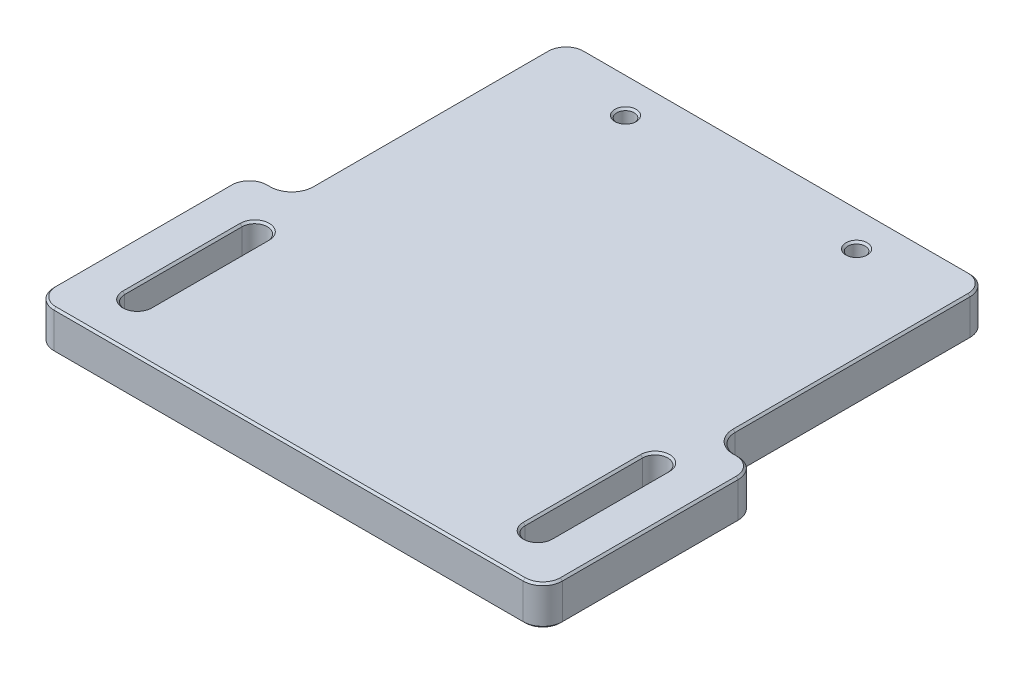
SolidWorks part; units mm, degrees
material "6061-T6 Al"
ref_plane "Front" through (0, 0, 0) normal (0, 0, 1) x (1, 0, 0)
ref_plane "Top" through (0, 0, 0) normal (0, 1, 0) x (1, 0, 0)
ref_plane "Right" through (0, 0, 0) normal (1, 0, 0) x (0, 0, -1)
sketch "Sketch1" plane through (0, 0, 0) normal (0, 1, 0) x (1, 0, 0)
  line L1 (0, 0) -> (-66, 0)
  line L2 (0, 0) -> (0, 63.5)
  line L3 (0, 63.5) -> (-66, 63.5)
  line L4 (-66, 0) -> (-66, 63.5)
  dimension "D1" = 66
  dimension "D2" = 63.5
extrude "Boss-Extrude1" add sketch "Sketch1" along normal blind 5.08
hole_wizard "#4 Clearance Hole1" positions "Sketch4" profile "Sketch3" hole size "#4" standard "Ansi Inch"
sketch "Sketch4" plane through (0, 5.08, 0) normal (0, 1, 0) x (-1, 0, 0)
  line L0 (66, 0) -> (0, 0) construction
  point P0 (59, -6.35)
  point P1 (7, -6.35)
  point P4 (33, 0)
  point P7 (33, 0)
  dimension "D1" = 26
  dimension "D2" = 26
  dimension "D3" = 6.35
sketch "Sketch3" plane through (-59, 5.08, -6.35) normal (1, 0, 0) x (0, 0, 1)
  line L0 (0, 0) -> (0, 26.3806)
  line L1 (0, 26.3806) -> (1.6319, 25.4)
  line L2 (1.6319, 25.4) -> (1.6319, 0)
  line L5 (1.6319, 0) -> (0, 0)
  line L10 (0, 26.3806) -> (-1.632, 25.4) construction
  line L11 (0, -6.35) -> (0, 107.95) construction
  dimension "Hole Dia." = 3.2639
  dimension "Hole Depth" = 25.4
  dimension "Drill Angle" = 118
sketch "Sketch6" plane through (0, 5.08, 0) normal (0, 1, 0) x (1, 0, 0)
  line L1 (-66, 63.5) -> (-60.5, 63.5)
  line L2 (-66, 63.5) -> (-66, 27.9109)
  line L3 (-66, 27.9109) -> (-60.5, 27.9109)
  line L4 (-60.5, 63.5) -> (-60.5, 27.9109)
  line L5 (0, 63.5) -> (-5.5, 63.5)
  line L6 (0, 63.5) -> (0, 27.9109)
  line L7 (0, 27.9109) -> (-5.5, 27.9109)
  line L8 (-5.5, 63.5) -> (-5.5, 27.9109)
  dimension "D1" = 55
  dimension "D2" = 35.5891
extrude "Cut-Extrude1" cut sketch "Sketch6" against normal blind 5.08
hole_wizard "#4-40 Tapped Hole1" positions "Sketch8" profile "Sketch7" tap size "#4-40" standard "Ansi Inch"
sketch "Sketch8" plane through (0, 5.08, 0) normal (0, 1, 0) x (-1, 0, 0)
  line L0 (66, 0) -> (0, 0) construction
  line L1 (5.5, -63.5) -> (60.5, -63.5) construction
  point P0 (48, -58.7375)
  point P1 (18, -58.7375)
  point P4 (33, 0)
  point P7 (33, 0)
  dimension "D1" = 15
  dimension "D2" = 15
  dimension "D3" = 4.7625
sketch "Sketch7" plane through (-48, 5.08, -58.7375) normal (1, 0, 0) x (0, 0, 1)
  line L0 (0, 0) -> (0, 8.2738)
  line L1 (0, 8.2738) -> (1.1303, 7.5946)
  line L2 (1.1303, 7.5946) -> (1.1303, 0)
  line L5 (1.1303, 0) -> (0, 0)
  line L10 (0, 8.2738) -> (-1.1303, 7.5946) construction
  line L11 (0, -6.35) -> (0, 107.95) construction
  dimension "Tap Drill Dia." = 2.2606
  dimension "Tap Drill Depth" = 7.5946
  dimension "Drill Angle" = 118
cosmetic thread "Hole Thread1" parameters "D1"=5.08, "D2"=2.8448
cosmetic thread "Hole Thread2" parameters "D1"=5.08, "D2"=2.8448
fillet "Fillet1" radius 2.54 6 edges at (-60.5, 2.54, -63.5) (-66, 2.54, 0) (0, 2.54, 0) (-5.5, 2.54, -63.5) (-5.5, 2.54, -27.9109) (-60.5, 2.54, -27.9109)
fillet "Fillet2" radius 2.54 2 edges at (0, 2.54, -27.9109) (-66, 2.54, -27.9109)
sketch "Sketch9" plane through (0, 5.08, 0) normal (0, 1, 0) x (1, 0, 0)
  line L0 (-59, 6.35) -> (-59, 21.59) construction
  line L1 (-60.6383, 6.35) -> (-60.6383, 21.59)
  line L2 (-57.3617, 6.35) -> (-57.3617, 21.59)
  line L3 (-7, 6.35) -> (-7, 21.59) construction
  line L4 (-8.6383, 6.35) -> (-8.6383, 21.59)
  line L5 (-5.3617, 6.35) -> (-5.3617, 21.59)
  line L6 (-63.46, 0) -> (-2.54, 0) construction
  arc A0 (-60.6383, 6.35) -> (-57.3617, 6.35) centre (-59, 6.35) ccw
  arc A1 (-57.3617, 21.59) -> (-60.6383, 21.59) centre (-59, 21.59) ccw
  arc A2 (-8.6383, 6.35) -> (-5.3617, 6.35) centre (-7, 6.35) ccw
  arc A3 (-5.3617, 21.59) -> (-8.6383, 21.59) centre (-7, 21.59) ccw
  point P2 (-59, 13.97)
  point P7 (-7, 13.97)
  point P16 (-33, 0)
  point P17 (-33, 0)
  dimension "D5" = 1.6383
  dimension "D6" = 1.6383
  dimension "D1" = 15.24
  dimension "D2" = 6.35
  dimension "D3" = 26
  dimension "D4" = 26
extrude "Cut-Extrude2" cut sketch "Sketch9" against normal through all
chamfer "Chamfer1" distance 0.254 angle 45 52 edges at (-65.2561, 0, -0.7439) (-33, 0, 0) (-0.7439, 0, -0.7439) (0, 0, -13.9554) (-0.7439, 0, -27.1669) (-2.75, 0, -27.9109) (-4.7561, 0, -28.6548) (-5.5, 0, -45.7054) (-6.2439, 0, -62.7561) (-33, 0, -63.5) (-59.7561, 0, -62.7561) (-60.5, 0, -45.7054) (-61.2439, 0, -28.6548) (-63.25, 0, -27.9109) (-65.2561, 0, -27.1669) (-66, 0, -13.9554) (-18, 0, -57.6072) (-48, 0, -57.6072) (-59, 0, -23.2283) (-57.3617, 0, -13.97) (-59, 0, -4.7117) (-60.6383, 0, -13.97) (-7, 0, -23.2283) (-5.3617, 0, -13.97) (-7, 0, -4.7117) (-8.6383, 0, -13.97) (-61.2439, 5.08, -28.6548) (-60.5, 5.08, -45.7054) (-59.7561, 5.08, -62.7561) (-33, 5.08, -63.5) (-6.2439, 5.08, -62.7561) (-5.5, 5.08, -45.7054) (-4.7561, 5.08, -28.6548) (-2.75, 5.08, -27.9109) (-0.7439, 5.08, -27.1669) (0, 5.08, -13.9554) (-0.7439, 5.08, -0.7439) (-33, 5.08, 0) (-65.2561, 5.08, -0.7439) (-66, 5.08, -13.9554) (-65.2561, 5.08, -27.1669) (-63.25, 5.08, -27.9109) (-18, 5.08, -57.6072) (-48, 5.08, -57.6072) (-57.3617, 5.08, -13.97) (-59, 5.08, -23.2283) (-60.6383, 5.08, -13.97) (-59, 5.08, -4.7117) (-5.3617, 5.08, -13.97) (-7, 5.08, -23.2283) (-8.6383, 5.08, -13.97) (-7, 5.08, -4.7117)
